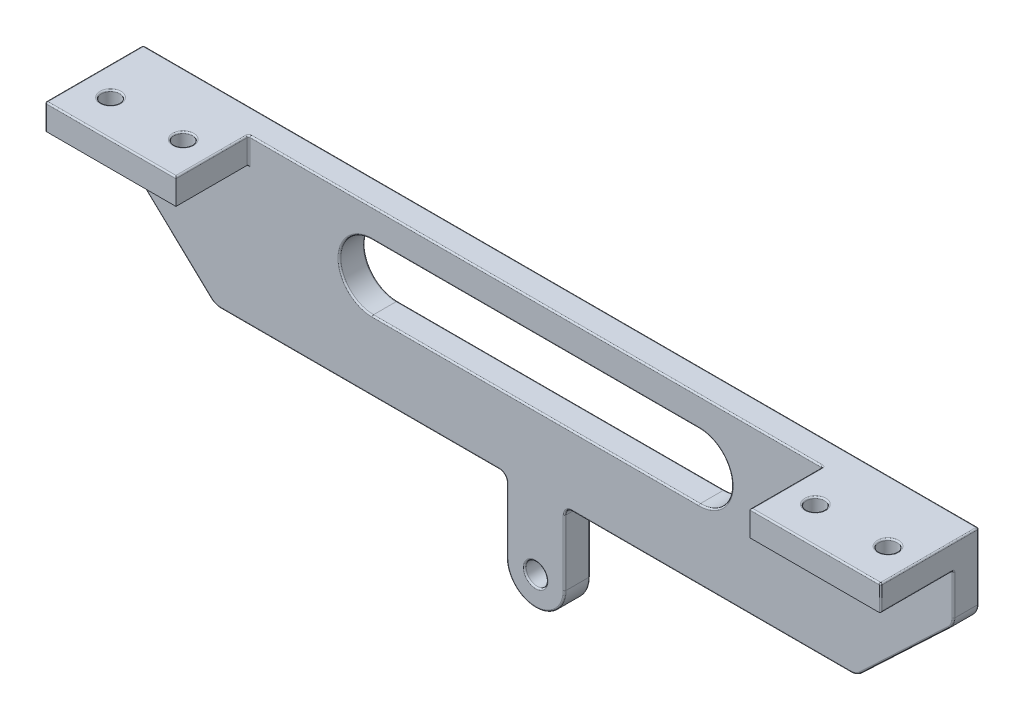
SolidWorks part; units mm, degrees
ref_plane "Front Plane" through (0, 0, 0) normal (0, 0, 1) x (1, 0, 0)
ref_plane "Top Plane" through (0, 0, 0) normal (0, 1, 0) x (1, 0, 0)
ref_plane "Right Plane" through (0, 0, 0) normal (1, 0, 0) x (0, 0, -1)
sketch "Sketch1" plane through (0, 0, 0) normal (0, 0, 1) x (1, 0, 0)
  line L0 (100, 0) -> (-100, 0)
  line L3 (-100, 0) -> (0, 100) construction
  line L4 (0, 100) -> (100, 0) construction
  line L5 (0, 0) -> (-50, 50) construction
  line L7 (0, 100) -> (0, 60) construction
  line L9 (-40, 60) -> (40, 60) construction
  circle A0 centre (-100, 0) radius 20
  circle A1 centre (0, 0) radius 20
  circle A2 centre (100, 0) radius 19.9987
  point P4 (0, 0)
  dimension "D5" = 40
  dimension "D6" = 39.9975
  dimension "D1" = 200
  dimension "D2" = 90
  dimension "D3" = 90
  dimension "D4" = 80
  dimension "D7" = 141.4214
  dimension "D8" = 70.7107
sketch "Sketch2" plane through (0, 0, 0) normal (0, 0, 1) x (1, 0, 0)
  line L0 (-56.5165, 43.4835) -> (-40, 60) construction
  line L1 (-100, 0) -> (0, 100) construction
  line L2 (-40, 60) -> (40, 60) construction
  line L3 (40, 60) -> (86.565, 13.435) construction
  line L4 (0, 100) -> (100, 0) construction
  line L5 (-49.4454, 36.4124) -> (-35.8579, 50)
  line L6 (-35.8579, 50) -> (35.8579, 50)
  line L7 (35.8579, 50) -> (79.4939, 6.364)
  line L8 (-63.5876, 50.5546) -> (-44.1421, 70)
  line L9 (-44.1421, 70) -> (44.1421, 70)
  line L10 (44.1421, 70) -> (93.636, 20.5061)
  line L11 (-63.5876, 50.5546) -> (-49.4454, 36.4124)
  line L12 (93.636, 20.5061) -> (79.4939, 6.364)
  line L13 (81.9688, 8.8388) -> (95.4038, -4.5962)
  line L14 (91.1612, 18.0312) -> (104.5962, 4.5962)
  line L15 (90.1005, 24.0416) -> (75.9584, 9.8995) construction
  line L16 (0, 100) -> (0, 60) construction
  line L17 (-6, 70) -> (-3.4486, 84.7178)
  line L18 (6, 70) -> (3.4486, 84.7178)
  circle A0 centre (100, 0) radius 3.5
  circle A1 centre (100, 0) radius 10 construction
  circle A3 centre (79.4939, 13.435) radius 1
  circle A4 centre (86.565, 20.5061) radius 1
  circle A5 centre (0, 60) radius 1.5
  circle A6 centre (0, 84.12) radius 1.5
  circle A8 centre (-50, 50) radius 1.5
  arc A9 (104.5962, 4.5962) -> (95.4038, -4.5962) centre (100, 0) cw
  arc A10 (-3.4486, 84.7178) -> (3.4486, 84.7178) centre (0, 84.12) cw
  point P51 (0, 70)
  dimension "D4" = 20
  dimension "D5" = 7
  dimension "D9" = 2
  dimension "D12" = 3
  dimension "D17" = 3
  dimension "D6" = 6.5
  dimension "D18" = 3
  dimension "D14" = 3.5
  dimension "D19" = 2
  dimension "D3" = 27.5
  dimension "D7" = 19
  dimension "D8" = 5
  dimension "D10" = 5
  dimension "D11" = 5
  dimension "D13" = 14.12
  dimension "D15" = 6
  dimension "D16" = 6
  dimension "D1" = 10
  dimension "D2" = 10
sketch "Sketch3" plane through (0, 0, 0) normal (0, 0, 1) x (1, 0, 0)
  line L0 (-86.565, 13.435) -> (-50, 50) construction
  line L1 (-100, 0) -> (0, 100) construction
  line L2 (-50, 50) -> (-13.435, 13.435) construction
  line L3 (0, 0) -> (-50, 50) construction
  line L4 (-79.4939, 6.364) -> (-50, 35.8579)
  line L5 (-50, 35.8579) -> (-20.5061, 6.364)
  line L6 (-93.636, 20.5061) -> (-50, 64.1421)
  line L7 (-50, 64.1421) -> (-6.364, 20.5061)
  line L10 (-91.1612, 18.0312) -> (-104.5962, 4.5962)
  line L11 (-81.9688, 8.8388) -> (-95.4038, -4.5962)
  line L12 (-18.0312, 8.8388) -> (-4.5962, -4.5962)
  line L13 (-8.8388, 18.0312) -> (4.5962, 4.5962)
  line L14 (-90.1005, 24.0416) -> (-75.9584, 9.8995) construction
  line L15 (-24.0416, 9.8995) -> (-9.8995, 24.0416) construction
  line L16 (-93.636, 20.5061) -> (-91.1612, 18.0312)
  line L17 (-79.4939, 6.364) -> (-81.9688, 8.8388)
  line L18 (-18.0312, 8.8388) -> (-20.5061, 6.364)
  line L19 (-6.364, 20.5061) -> (-8.8388, 18.0312)
  circle A0 centre (-100, 0) radius 10 construction
  circle A1 centre (-100, 0) radius 3.5
  circle A2 centre (0, 0) radius 10 construction
  circle A3 centre (0, 0) radius 3.5
  circle A6 centre (-86.565, 20.5061) radius 1
  circle A7 centre (-79.4939, 13.435) radius 1
  circle A8 centre (-13.435, 20.5061) radius 1
  circle A9 centre (-20.5061, 13.435) radius 1
  circle A10 centre (-50, 50) radius 1.5 construction
  circle A11 centre (-50, 50) radius 1.5
  arc A12 (4.5962, 4.5962) -> (-4.5962, -4.5962) centre (0, 0) cw
  arc A13 (-104.5962, 4.5962) -> (-95.4038, -4.5962) centre (-100, 0) ccw
  dimension "D1" = 20
  dimension "D2" = 7
  dimension "D9" = 2
  dimension "D13" = 2
  dimension "D3" = 6.5
  dimension "D16" = 3
  dimension "D17" = 3
  dimension "D18" = 6.5
  dimension "D6" = 19
  dimension "D7" = 3.5
  dimension "D8" = 19
  dimension "D10" = 5
  dimension "D11" = 5
  dimension "D12" = 3.5
  dimension "D14" = 5
  dimension "D15" = 5
  dimension "D19" = 5
  dimension "D20" = 5
  dimension "D4" = 10
  dimension "D5" = 10
sketch "Sketch4" plane through (0, 0, 0) normal (0, 0, 1) x (1, 0, 0)
  line L6 (-57.5, 92.6154) -> (57.5, 92.6154)
  line L7 (57.5, 92.6154) -> (57.5, 82.6154)
  line L8 (57.5, 82.6154) -> (44.1421, 70)
  line L9 (44.1421, 70) -> (-44.1421, 70)
  line L10 (-44.1421, 70) -> (-57.5, 82.6154)
  line L11 (-57.5, 82.6154) -> (-57.5, 92.6154)
  line L12 (-4, 60) -> (-4, 70)
  line L13 (4, 60) -> (4, 70)
  line L14 (-22.5, 84.1154) -> (22.5, 84.1154) construction
  line L15 (-22.5, 88.6154) -> (22.5, 88.6154)
  line L16 (-22.5, 79.6154) -> (22.5, 79.6154)
  arc A0 (-4, 60) -> (4, 60) centre (0, 60) ccw
  arc A1 (-22.5, 88.6154) -> (-22.5, 79.6154) centre (-22.5, 84.1154) ccw
  circle A2 centre (0, 60) radius 1.5 construction
  arc A4 (22.5, 79.6154) -> (22.5, 88.6154) centre (22.5, 84.1154) ccw
  point P2 (0, 92.6154)
  point P15 (0, 84.1154)
  dimension "D3" = 4
  dimension "D8" = 2.5
  dimension "D1" = 115
  dimension "D2" = 10
  dimension "D4" = 45
  dimension "D5" = 9
  dimension "D6" = 12.6154
  dimension "D7" = 4
sketch "Sketch5" plane through (0, 0, 0) normal (0, 0, 1) x (1, 0, 0)
  line L0 (-4, 60) -> (-4, 70) construction
  line L1 (4, 60) -> (4, 70) construction
  line L2 (22.5, 88.6154) -> (-22.5, 88.6154)
  line L3 (-22.5, 79.6154) -> (22.5, 79.6154)
  line L4 (22.5, 88.6154) -> (-22.5, 88.6154)
  line L5 (-22.5, 79.6154) -> (22.5, 79.6154)
  line L6 (57.5, 92.6154) -> (-57.5, 92.6154)
  line L7 (57.5, 82.6154) -> (57.5, 92.6154)
  line L8 (44.1421, 70) -> (57.5, 82.6154)
  line L9 (-44.1421, 70) -> (44.1421, 70)
  line L10 (-57.5, 82.6154) -> (-44.1421, 70)
  line L11 (-57.5, 92.6154) -> (-57.5, 82.6154)
  line L12 (57.5, 92.6154) -> (-57.5, 92.6154)
  line L13 (57.5, 82.6154) -> (57.5, 92.6154)
  line L14 (44.1421, 70) -> (57.5, 82.6154)
  line L16 (-57.5, 82.6154) -> (-44.1421, 70)
  line L17 (-57.5, 92.6154) -> (-57.5, 82.6154)
  line L18 (-4, 60) -> (-4, 70)
  line L19 (4, 60) -> (4, 70)
  line L20 (44.1421, 70) -> (4, 70)
  line L21 (-4, 70) -> (-44.1421, 70)
  arc A0 (-4, 60) -> (4, 60) centre (0, 60) ccw construction
  arc A1 (-4, 60) -> (4, 60) centre (0, 60) ccw
  arc A2 (22.5, 79.6154) -> (22.5, 88.6154) centre (22.5, 84.1154) ccw
  arc A3 (-22.5, 88.6154) -> (-22.5, 79.6154) centre (-22.5, 84.1154) ccw
  arc A4 (22.5, 79.6154) -> (22.5, 88.6154) centre (22.5, 84.1154) ccw
  arc A5 (-22.5, 88.6154) -> (-22.5, 79.6154) centre (-22.5, 84.1154) ccw
  circle A6 centre (0, 60) radius 1.5
  dimension "D3" = 3
  dimension "D1" = 0
  dimension "D2" = 0
extrude "Boss-Extrude1" add sketch "Sketch5" along normal blind 3.5
sketch "Sketch6" plane through (0, 92.6154, 0) normal (0, 1, 0) x (1, 0, 0)
  line L0 (57.5, -3.5) -> (57.5, -13.5)
  line L1 (57.5, -13.5) -> (39.5, -13.5)
  line L2 (39.5, -13.5) -> (39.5, -3.5)
  line L3 (57.5, -3.5) -> (-57.5, -3.5) construction
  line L4 (39.5, -3.5) -> (57.5, -3.5)
  line L5 (57.5, -8.5) -> (39.5, -8.5) construction
  line L6 (48.5, -8.5) -> (48.5, -13.5) construction
  line L7 (0, -3.5) -> (0, -26.464) construction
  line L8 (-48.5, -8.5) -> (-48.5, -13.5) construction
  line L9 (-57.5, -8.5) -> (-39.5, -8.5) construction
  line L10 (-39.5, -3.5) -> (-57.5, -3.5)
  line L11 (-39.5, -13.5) -> (-39.5, -3.5)
  line L12 (-57.5, -13.5) -> (-39.5, -13.5)
  line L13 (-57.5, -3.5) -> (-57.5, -13.5)
  circle A0 centre (53.5, -8.5) radius 1.25
  circle A1 centre (43.5, -8.5) radius 1.25
  circle A2 centre (-43.5, -8.5) radius 1.25
  circle A3 centre (-53.5, -8.5) radius 1.25
  dimension "D4" = 2.5
  dimension "D1" = 18
  dimension "D2" = 10
  dimension "D3" = 10
extrude "Boss-Extrude2" add sketch "Sketch6" against normal blind 3.5
fillet "Fillet1" radius 2 4 edges at (-44.1421, 70, 1.75) (-57.5, 82.6154, 1.75) (44.1421, 70, 1.75) (57.5, 82.6154, 1.75)
fillet "Fillet2" radius 1 2 edges at (4, 70, 1.75) (-4, 70, 1.75)
fillet "Fillet3" radius 0.2 60 edges at (-53.5, 92.6154, 7.25) (-43.5, 92.6154, 7.25) (-39.5, 92.6154, 8.5) (-48.5, 92.6154, 13.5) (-48.5, 89.1154, 3.5) (-57.5, 89.1154, 8.5) (-39.5, 90.8654, 3.5) (-57.5, 90.8654, 13.5) (43.5, 92.6154, 9.75) (53.5, 92.6154, 9.75) (39.5, 92.6154, 8.5) (48.5, 92.6154, 13.5) (48.5, 89.1154, 3.5) (57.5, 89.1154, 8.5) (39.5, 90.8654, 3.5) (57.5, 90.8654, 13.5) (1.5, 60, 0) (1.5, 60, 3.5) (-27, 84.1154, 0) (0, 79.6154, 0) (27, 84.1154, 0) (0, 88.6154, 0) (-27, 84.1154, 3.5) (0, 79.6154, 3.5) (0, 88.6154, 3.5) (-57.5, 88.0465, 0) (-50.7967, 76.2847, 0) (-24.1735, 70, 0) (-4, 64.5, 0) (0, 56, 0) (4, 64.5, 0) (24.1735, 70, 0) (50.7967, 76.2847, 0) (57.5, 88.0465, 0) (0, 92.6154, 0) (-57.5, 86.2965, 3.5) (-50.7967, 76.2847, 3.5) (-24.1735, 70, 3.5) (-4, 64.5, 3.5) (0, 56, 3.5) (4, 64.5, 3.5) (24.1735, 70, 3.5) (50.7967, 76.2847, 3.5) (57.5, 86.2965, 3.5) (0, 92.6154, 3.5) (-57.5, 92.6154, 6.75) (57.5, 92.6154, 6.75) (57.3366, 82.6858, 0) (44.0859, 70.1415, 0) (-57.3366, 82.6858, 0) (-44.0859, 70.1415, 0) (57.3366, 82.6858, 3.5) (44.0859, 70.1415, 3.5) (-57.3366, 82.6858, 3.5) (-44.0859, 70.1415, 3.5) (4.2929, 69.7071, 0) (4.2929, 69.7071, 3.5) (-4.2929, 69.7071, 0) (-4.2929, 69.7071, 3.5) (27, 84.1154, 3.5)
